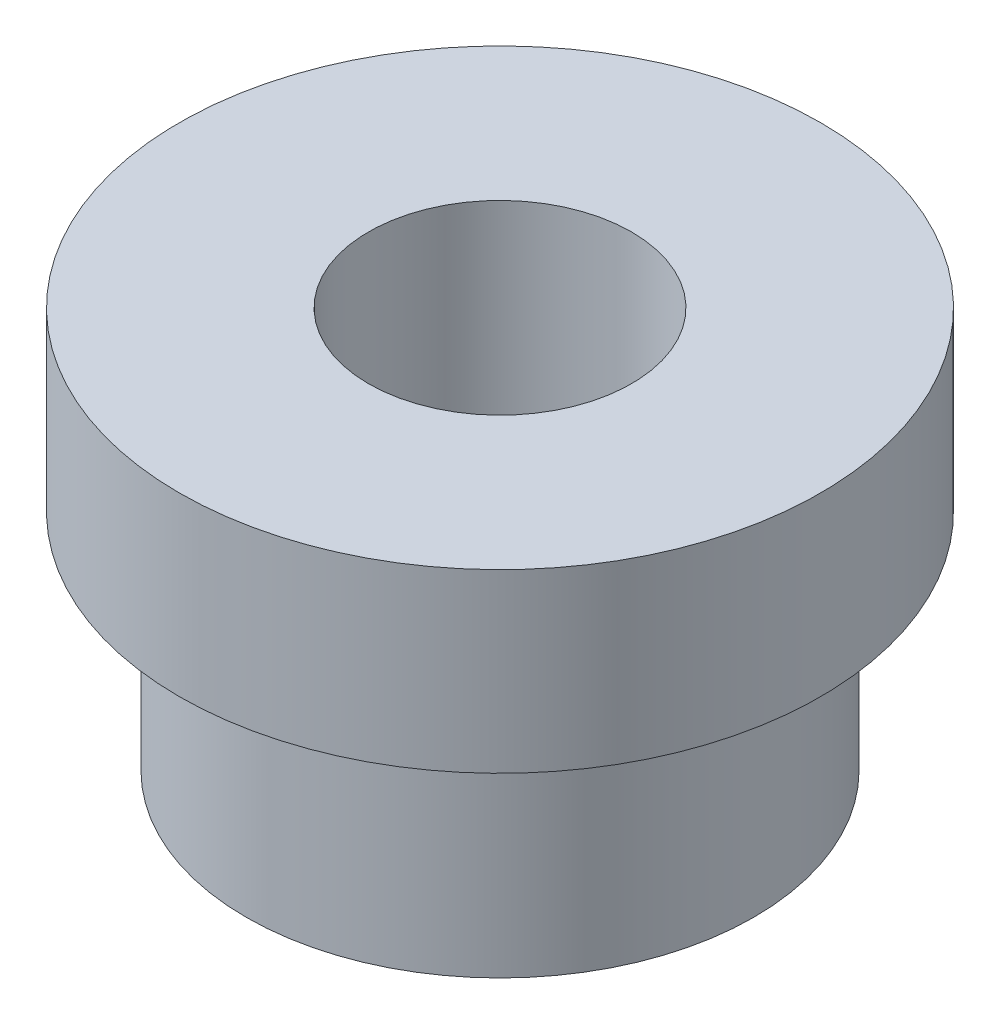
SolidWorks part; units mm, degrees
material "Inconel 718"
ref_plane "Front Plane" through (0, 0, 0) normal (0, 0, 1) x (1, 0, 0)
ref_plane "Top Plane" through (0, 0, 0) normal (0, 1, 0) x (1, 0, 0)
ref_plane "Right Plane" through (0, 0, 0) normal (1, 0, 0) x (0, 0, -1)
sketch "Sketch3" plane through (0, 0, 0) normal (0, 0, 1) x (1, 0, 0)
  line L0 (0, 17.78) -> (0, 23.0435) construction
  line L1 (0, 0) -> (12.065, 0)
  line L2 (0, 0) -> (0, 19.05)
  line L3 (12.065, 0) -> (12.065, 10.668)
  line L4 (12.065, 10.668) -> (15.24, 10.668)
  line L5 (15.24, 10.668) -> (15.24, 19.05)
  line L7 (0, 19.05) -> (15.24, 19.05)
  dimension "D1" = 12.065
  dimension "D2" = 10.668
  dimension "D3" = 19.05
  dimension "D5" = 15.24
revolve "Revolve1" add sketch "Sketch3" angle 360 about L0
cosmetic thread "Cosmetic Thread1" parameters "D1"=6.35, "D2"=18.8646
hole_wizard "M14x1.5 Tapped Hole1" positions "Sketch4" profile "Sketch6" tap size "M14x1.5" standard "ANSI Metric" end condition through all
sketch "Sketch4" plane through (0, 19.05, 0) normal (0, 1, 0) x (1, 0, 0)
  point P0 (0, 0)
sketch "Sketch6" plane through (0, 19.05, 0) normal (1, 0, 0) x (0, 0, 1)
  line L0 (0, 0) -> (0, 19.05)
  line L1 (0, 19.05) -> (6.25, 19.05)
  line L2 (6.25, 19.05) -> (6.25, 0)
  line L5 (6.25, 0) -> (0, 0)
  line L11 (0, -6.35) -> (0, 107.95) construction
  dimension "Thru Tap Drill Dia." = 12.5
  dimension "Thru Tap Drill Depth" = 19.05
cosmetic thread "Hole Thread1" parameters "D2"=14
